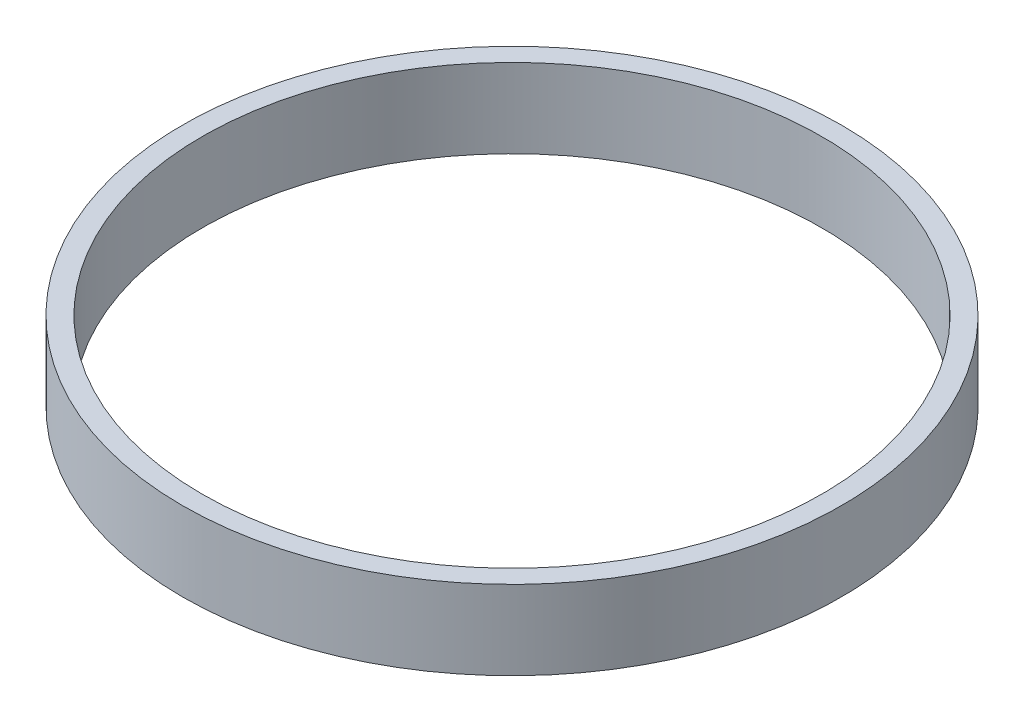
SolidWorks part; units mm, degrees
ref_plane "Front Plane" through (0, 0, 0) normal (0, 0, 1) x (1, 0, 0)
ref_plane "Top Plane" through (0, 0, 0) normal (0, 1, 0) x (1, 0, 0)
ref_plane "Right Plane" through (0, 0, 0) normal (1, 0, 0) x (0, 0, -1)
sketch "Sketch1" plane through (0, 0, 0) normal (0, 1, 0) x (1, 0, 0)
  circle A1 centre (0, 0) radius 25
  circle A2 centre (0, 0) radius 23.5
extrude "Boss-Extrude1" add sketch "Sketch1" along normal blind 6 separate body
